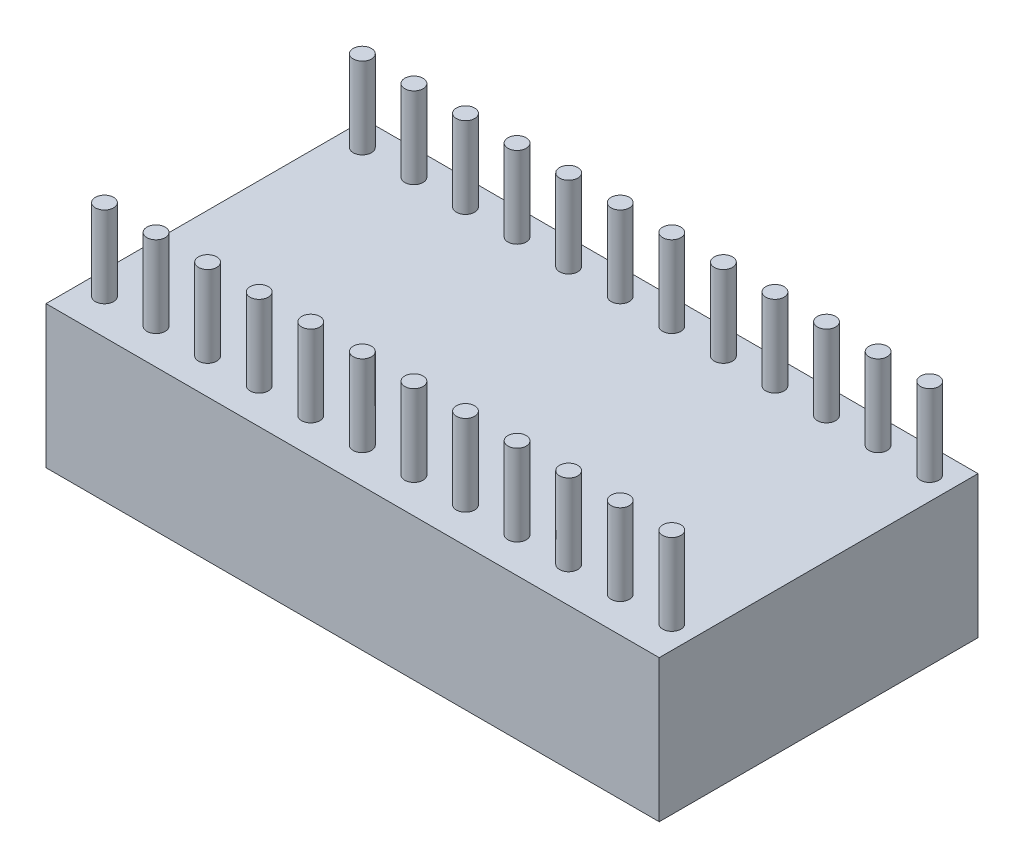
SolidWorks part; units mm, degrees
ref_plane "Front Plane" through (0, 0, 0) normal (0, 0, 1) x (1, 0, 0)
ref_plane "Top Plane" through (0, 0, 0) normal (0, 1, 0) x (1, 0, 0)
ref_plane "Right Plane" through (0, 0, 0) normal (1, 0, 0) x (0, 0, -1)
sketch "Sketch1" plane through (0, 0, 0) normal (0, 1, 0) x (1, 0, 0)
  line L1 (0, 0) -> (30.2, 0)
  line L2 (0, 0) -> (0, -15.7)
  line L3 (0, -15.7) -> (30.2, -15.7)
  line L4 (30.2, 0) -> (30.2, -15.7)
  dimension "D1" = 30.2
  dimension "D2" = 15.7
extrude "Boss-Extrude1" add sketch "Sketch1" along normal blind 7
sketch "Sketch2" plane through (0, 7, 0) normal (0, 1, 0) x (1, 0, 0)
  line L6 (30.2, 0) -> (0, 0) construction
  line L20 (-1.9561, -7.6) -> (32.7722, -7.6) construction
  line L37 (4.94, 1.0526) -> (4.94, -2.6375) construction
  line L58 (10.02, 0.8494) -> (10.02, -2.7605) construction
  line L60 (20.18, 0.8494) -> (20.18, -3.0708) construction
  circle A0 centre (1.13, -1.25) radius 0.45
  circle A1 centre (3.67, -1.25) radius 0.45
  circle A2 centre (6.21, -1.25) radius 0.45
  circle A3 centre (8.75, -1.25) radius 0.45
  circle A4 centre (11.29, -1.25) radius 0.45
  circle A5 centre (13.83, -1.25) radius 0.45
  circle A6 centre (16.37, -1.25) radius 0.45
  circle A7 centre (18.91, -1.25) radius 0.45
  circle A8 centre (21.45, -1.25) radius 0.45
  circle A9 centre (23.99, -1.25) radius 0.45
  circle A10 centre (26.53, -1.25) radius 0.45
  circle A11 centre (29.07, -1.25) radius 0.45
  circle A12 centre (29.07, -13.95) radius 0.45
  circle A13 centre (26.53, -13.95) radius 0.45
  circle A14 centre (23.99, -13.95) radius 0.45
  circle A15 centre (21.45, -13.95) radius 0.45
  circle A16 centre (18.91, -13.95) radius 0.45
  circle A17 centre (16.37, -13.95) radius 0.45
  circle A18 centre (13.83, -13.95) radius 0.45
  circle A19 centre (11.29, -13.95) radius 0.45
  circle A20 centre (8.75, -13.95) radius 0.45
  circle A21 centre (6.21, -13.95) radius 0.45
  circle A22 centre (3.67, -13.95) radius 0.45
  circle A23 centre (1.13, -13.95) radius 0.45
  dimension "D1" = 0.9
  dimension "D2" = 0.9
  dimension "D3" = 1.13
  dimension "D4" = 1.25
  dimension "D5" = 1.25
  dimension "D6" = 2.54
  dimension "D7" = 7.6
  dimension "D8" = 1.27
  dimension "D9" = 1.27
  dimension "D10" = 1.27
extrude "Boss-Extrude2" add sketch "Sketch2" along normal blind 4
